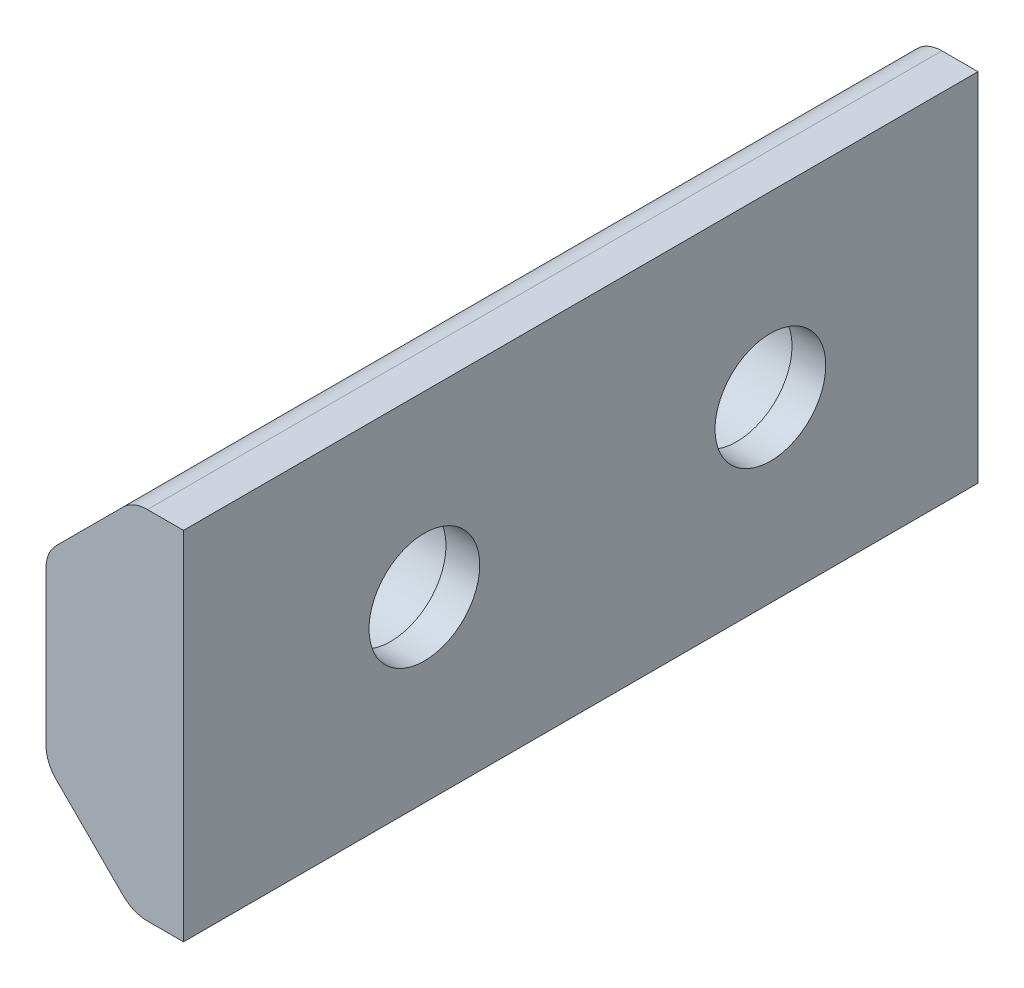
SolidWorks part; units mm, degrees
ref_plane "Front Plane" through (0, 0, 0) normal (0, 0, 1) x (1, 0, 0)
ref_plane "Top Plane" through (0, 0, 0) normal (0, 1, 0) x (1, 0, 0)
ref_plane "Right Plane" through (0, 0, 0) normal (1, 0, 0) x (0, 0, -1)
sketch "Sketch1" plane through (0, 0, 0) normal (0, 0, 1) x (1, 0, 0)
  line L0 (1.9338, 5.15) -> (1.9338, -5.15)
  line L1 (1.9338, -5.15) -> (0.4765, -5.15)
  line L2 (0.4765, -5.15) -> (-2.0404, -2.6331)
  line L3 (-2.0404, -2.6331) -> (-2.0404, 2.6331)
  line L4 (-2.0404, 2.6331) -> (0.4765, 5.15)
  line L5 (0.4765, 5.15) -> (1.9338, 5.15)
  line L6 (1.9338, 0) -> (0, 0) construction
  line L7 (0, 0) -> (-2.0404, 0) construction
  line L8 (0.4765, 5.15) -> (0.4765, -5.15) construction
  dimension "D1" = 10.3
  dimension "D2" = 5.2663
extrude "Boss-Extrude1" add sketch "Sketch1" along normal blind 36
sketch "Sketch2" plane through (1.9338, 0, 0) normal (1, 0, 0) x (0, 0, -1)
  line L0 (-36, 0) -> (-31, 0) construction
  line L1 (-31, 0) -> (-16, 0) construction
  line L2 (-16, 0) -> (-16, 5.15) construction
  line L3 (-36, 5.15) -> (0, 5.15) construction
  line L4 (-36, -5.15) -> (-36, 5.15) construction
  line L5 (-6, 0) -> (-6, 0.6373) construction
  line L6 (-16, 0) -> (0, 0) construction
  line L7 (-6, 0.6373) -> (0, 0.6373) construction
  line L8 (0, -5.15) -> (0, 5.15) construction
  circle A0 centre (-16, 0) radius 1.6
  circle A1 centre (-31, 0) radius 1.6
  circle A2 centre (-6, 0) radius 1.6
  dimension "D1" = 3.2
  dimension "D2" = 5
  dimension "D3" = 5.15
  dimension "D4" = 15
  dimension "D5" = 6
extrude "Cut-Extrude1" cut sketch "Sketch2" against normal blind 10
sketch "Sketch3" plane through (-2.0404, 0, 0) normal (-1, 0, 0) x (0, 0, 1)
  circle A0 centre (16, 0) radius 1.95
  circle A1 centre (31, 0) radius 1.95
  circle A2 centre (6, 0) radius 1.95
  dimension "D1" = 3.9
extrude "Cut-Extrude2" cut sketch "Sketch3" against normal blind 3
fillet "Fillet1" radius 1
sketch "Sketch4" plane through (1.9338, 0, 0) normal (1, 0, 0) x (0, 0, -1)
  line L0 (-36, -5.15) -> (0, -5.15) construction
  line L1 (-36, 5.15) -> (-28, 5.15)
  line L2 (-36, 5.15) -> (-36, -5.15)
  line L3 (-36, -5.15) -> (-28, -5.15)
  line L4 (-28, 5.15) -> (-28, -5.15)
  dimension "D1" = 8
extrude "Cut-Extrude3" cut sketch "Sketch4" against normal blind 10
sketch "Sketch5" plane through (1.9338, 0, 0) normal (1, 0, 0) x (0, 0, -1)
  line L0 (-28, -5.15) -> (0, -5.15) construction
  line L1 (-28, 5.15) -> (-22.9606, 5.15)
  line L2 (-28, 5.15) -> (-28, -5.15)
  line L3 (-28, -5.15) -> (-22.9606, -5.15)
  line L4 (-22.9606, 5.15) -> (-22.9606, -5.15)
  line L5 (-22.9606, 10.1958) -> (-22.9606, -10.3042) construction
extrude "Cut-Extrude4" cut sketch "Sketch5" against normal blind 10
